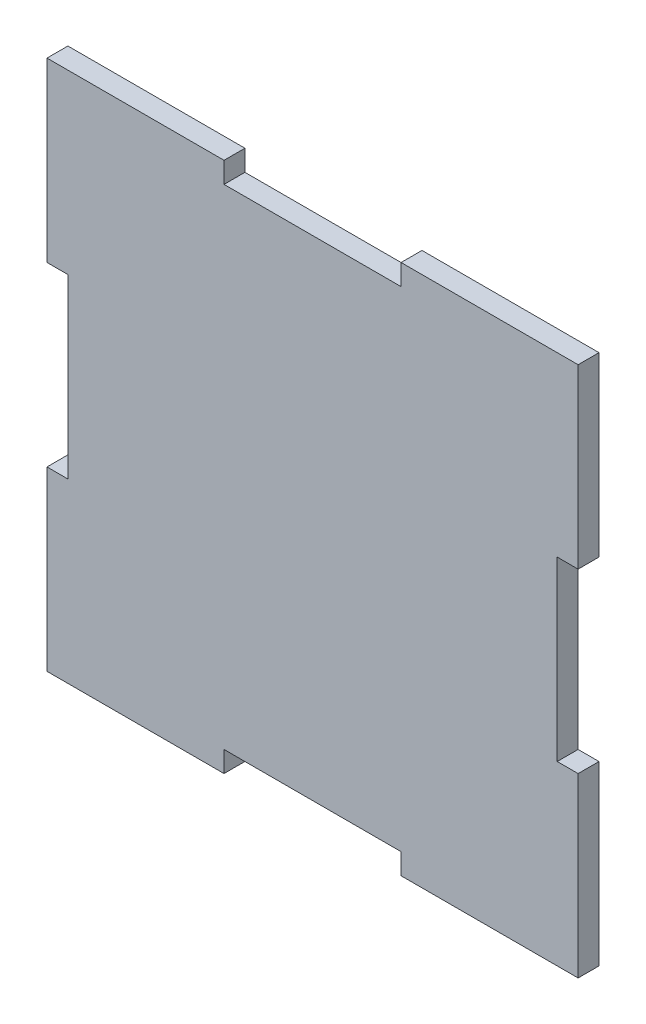
SolidWorks part; units mm, degrees
ref_plane "Front Plane" through (0, 0, 0) normal (0, 0, 1) x (1, 0, 0)
ref_plane "Top Plane" through (0, 0, 0) normal (0, 1, 0) x (1, 0, 0)
ref_plane "Right Plane" through (0, 0, 0) normal (1, 0, 0) x (0, 0, -1)
sketch "bottom outline" plane through (0, 0, 0) normal (0, 0, 1) x (1, 0, 0)
  line L0 (0, 50.8) -> (0, 76.2)
  line L1 (0, 0) -> (25.4, 0)
  line L2 (0, 0) -> (0, 25.4)
  line L3 (0, 76.2) -> (25.4, 76.2)
  line L4 (76.2, 0) -> (76.2, 25.4)
  line L5 (0, 50.8) -> (2.9972, 50.8)
  line L6 (50.8, 76.2) -> (76.2, 76.2)
  line L7 (0, 25.4) -> (2.9972, 25.4)
  line L8 (2.9972, 50.8) -> (2.9972, 25.4)
  line L9 (76.2, 50.8) -> (73.2028, 50.8)
  line L10 (50.8, 0) -> (76.2, 0)
  line L11 (76.2, 25.4) -> (73.2028, 25.4)
  line L12 (73.2028, 50.8) -> (73.2028, 25.4)
  line L14 (50.8, 0) -> (50.8, 2.9972)
  line L15 (50.8, 2.9972) -> (25.4, 2.9972)
  line L16 (25.4, 0) -> (25.4, 2.9972)
  line L17 (76.2, 50.8) -> (76.2, 76.2)
  line L18 (25.4, 76.2) -> (25.4, 73.2028)
  line L19 (25.4, 73.2028) -> (50.8, 73.2028)
  line L20 (50.8, 76.2) -> (50.8, 73.2028)
  dimension "tabDepth" = 2.9972
  dimension "width" = 76.2
  dimension "length" = 76.2
extrude "plate" add sketch "bottom outline" along normal blind 2.9972
equation "\"drawerLength\"= 3"
equation "\"drawerWidth\"= 3"
